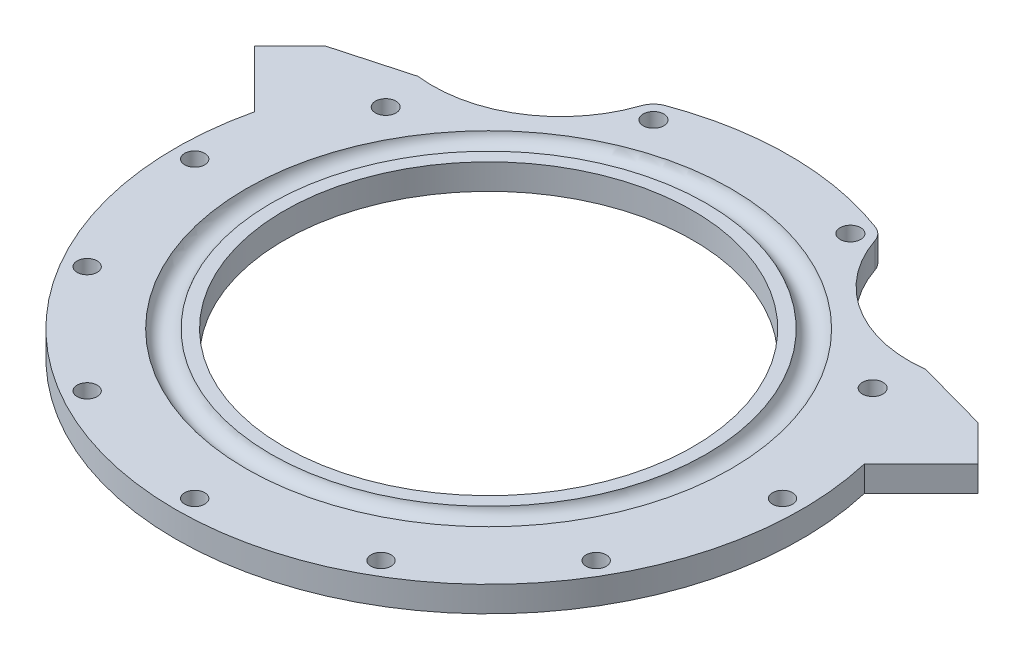
SolidWorks part; units mm, degrees
material "Alum Plate"
ref_plane "Front Plane" through (0, 0, 0) normal (0, 0, 1) x (1, 0, 0)
ref_plane "Top Plane" through (0, 0, 0) normal (0, 1, 0) x (1, 0, 0)
ref_plane "Right Plane" through (0, 0, 0) normal (1, 0, 0) x (0, 0, -1)
other "Bounding Box"
ref_plane "Default Plane" through (-8.9266, -12.7485, 0) normal (-0.1736, 0.9848, 0) x (0.9848, 0.1736, 0)
sketch "Sketch1" plane through (0, 0, 0) normal (0, 1, 0) x (1, 0, 0)
  circle A0 centre (0, 0) radius 50.8
  circle A1 centre (0, 0) radius 63.5
  dimension "D1" = 101.6
  dimension "D2" = 127
extrude "Boss-Extrude1" add sketch "Sketch1" along normal mid plane 6.35
sketch "Sketch2" plane through (0, 0, 0) normal (0, 0, 1) x (1, 0, 0)
  line L0 (57.15, 3.81) -> (63.5, 3.81) construction
  line L1 (63.5, 3.81) -> (63.5, 3.175) construction
  line L2 (0, 0) -> (0, 13.9971) construction
  circle A0 centre (57.15, 3.81) radius 3.175
  dimension "D1" = 6.35
  dimension "D2" = 6.35
  dimension "D3" = 0.635
revolve "Cut-Revolve1" cut sketch "Sketch2" angle 360 about L2
sketch "Sketch3" plane through (0, -3.175, 0) normal (0, -1, 0) x (1, 0, 0)
  circle A0 centre (0, 0) radius 63.5 construction
  circle A1 centre (0, 0) radius 63.5
  circle A2 centre (0, 0) radius 77.7875
  dimension "D1" = 155.575
extrude "Boss-Extrude2" add sketch "Sketch3" against normal through all
sketch "Sketch4" plane through (0, 3.175, 0) normal (0, 1, 0) x (1, 0, 0)
  line L0 (0, -77.7875) -> (0, -73.025) construction
  circle A0 centre (0, -73.025) radius 2.4892
  circle A1 centre (0, 0) radius 77.7875 construction
  dimension "D1" = 4.9784
  dimension "D2" = 4.7625
extrude "Cut-Extrude1" cut sketch "Sketch4" against normal through all
pattern_circular "CirPattern1" count 12 over 360 about axis through (0, 0, 0) along (0, 1, 0) skipping 4, 5, 6, 7, 8 of "Cut-Extrude1"
sketch "Sketch5" plane through (0, 3.175, 0) normal (0, 1, 0) x (1, 0, 0)
  line L0 (0, 0) -> (-66.0227, -66.0227) construction
  line L1 (0, 0) -> (27.7565, -27.7565) construction
  line L2 (0, 0) -> (0, 21.5705) construction
  line L3 (74.8954, 21.0138) -> (87.7371, 33.8556)
  line L4 (87.7371, 33.8556) -> (81.0019, 40.5908)
  line L5 (81.0019, 40.5908) -> (71.364, 30.9528)
  line L6 (-71.364, 30.9528) -> (-81.0019, 40.5908)
  line L7 (-81.0019, 40.5908) -> (-87.7371, 33.8556)
  line L8 (-87.7371, 33.8556) -> (-74.8954, 21.0138)
  arc A0 (74.8954, 21.0138) -> (71.364, 30.9528) centre (0, 0) ccw
  circle A1 centre (0, 0) radius 77.7875 construction
  arc A2 (-74.8954, 21.0138) -> (-71.364, 30.9528) centre (0, 0) cw
  dimension "D1" = 45
  dimension "D2" = 38.1
  dimension "D3" = 9.525
  dimension "D4" = 18.161
extrude "Boss-Extrude3" add sketch "Sketch5" against normal through all
sketch "Sketch6" plane through (0, 3.175, 0) normal (0, 1, 0) x (1, 0, 0)
  line L0 (0, 0) -> (59.1288, 77.0581) construction
  line L1 (0, 0) -> (0, 26.4948) construction
  circle A0 centre (59.1288, 77.0581) radius 31.75
  dimension "D1" = 63.5
  dimension "D2" = 97.1296
  dimension "D3" = 37.5
extrude "Cut-Extrude2" cut sketch "Sketch6" against normal through all
sketch "Sketch7" plane through (0, 3.175, 0) normal (0, 1, 0) x (1, 0, 0)
  line L0 (-67.366, 38.8938) -> (-60.4919, 34.925) construction
  line L1 (-27.2418, 72.8614) -> (-24.462, 65.4266) construction
  line L2 (24.462, 65.4266) -> (27.2418, 72.8614) construction
  line L3 (60.4919, 34.925) -> (67.366, 38.8938) construction
  line L4 (-24.462, 65.4266) -> (24.462, 65.4266) construction
  line L5 (60.4919, 34.925) -> (-60.4919, 34.925) construction
  line L6 (-60.4919, 34.925) -> (0, 0) construction
  line L7 (0, 0) -> (-24.462, 65.4266) construction
  line L8 (-77.7875, 0) -> (0, 0) construction
  line L9 (0, 0) -> (0, 90.3017) construction
  line L10 (60.4919, 34.925) -> (54.9926, 31.75) construction
  circle A0 centre (-24.462, 65.4266) radius 2.5527
  circle A1 centre (-60.4919, 34.925) radius 2.5527
  circle A2 centre (24.462, 65.4266) radius 2.5527
  circle A3 centre (60.4919, 34.925) radius 2.5527
  arc A4 (27.6798, 72.6961) -> (-71.364, 30.9528) centre (0, 0) ccw construction
  arc A5 (71.364, 30.9528) -> (63.055, 45.5518) centre (0, 0) ccw construction
  circle A6 centre (0, 0) radius 63.5 construction
  arc A7 (-74.8954, 21.0138) -> (74.8954, 21.0138) centre (0, 0) ccw construction
  dimension "D2" = 5.1054
  dimension "D1" = 6.35
  dimension "D3" = 20.5
  dimension "D4" = 30
extrude "Cut-Extrude3" cut sketch "Sketch7" against normal through all
sketch "Sketch9" plane through (0, 3.175, 0) normal (0, 1, 0) x (1, 0, 0)
  line L4 (75.7676, 17.6115) -> (73.6303, 19.7488)
  line L5 (75.7676, 17.6115) -> (89.8744, 31.7183)
  line L6 (73.6303, 19.7488) -> (87.7371, 33.8556)
  line L7 (89.8744, 31.7183) -> (87.7371, 33.8556)
  line L8 (74.8954, 21.0138) -> (87.7371, 33.8556) construction
  line L9 (81.0019, 40.5908) -> (63.055, 45.5518)
  line L10 (63.055, 45.5518) -> (71.364, 30.9528)
  line L11 (71.364, 30.9528) -> (81.0019, 40.5908)
  arc A0 (-74.8954, 21.0138) -> (74.8954, 21.0138) centre (0, 0) ccw construction
  dimension "D1" = 3.0226
extrude "Boss-Extrude4" add sketch "Sketch9" against normal through all
mirror "Mirror1" about plane through (0, 0, 0) normal (1, 0, 0) of "Boss-Extrude4", "Cut-Extrude2"
sketch "Sketch8" plane through (0, -3.175, 0) normal (0, -1, 0) x (1, 0, 0)
  arc A0 (-29.0279, -66.9585) -> (-26.1486, -69.9376) centre (-24.462, -65.4266) ccw
  arc A1 (26.1486, -69.9376) -> (29.0279, -66.9585) centre (24.462, -65.4266) ccw
  arc A2 (63.055, -45.5518) -> (27.6798, -72.6961) centre (59.1288, -77.0581) ccw construction
  arc A3 (-27.6798, -72.6961) -> (-63.055, -45.5518) centre (-59.1288, -77.0581) ccw construction
  arc A4 (-26.1486, -69.9376) -> (26.1486, -69.9376) centre (0, 0) ccw
  arc A5 (-27.6798, -72.6961) -> (27.6798, -72.6961) centre (0, 0) ccw construction
  arc A6 (29.0279, -66.9585) -> (27.6798, -72.6961) centre (59.1288, -77.0581) ccw
  arc A7 (-27.6798, -72.6961) -> (27.6798, -72.6961) centre (0, 0) ccw
  arc A8 (-27.6798, -72.6961) -> (-29.0279, -66.9585) centre (-59.1288, -77.0581) ccw
extrude "Cut-Extrude4" cut sketch "Sketch8" against normal through all
